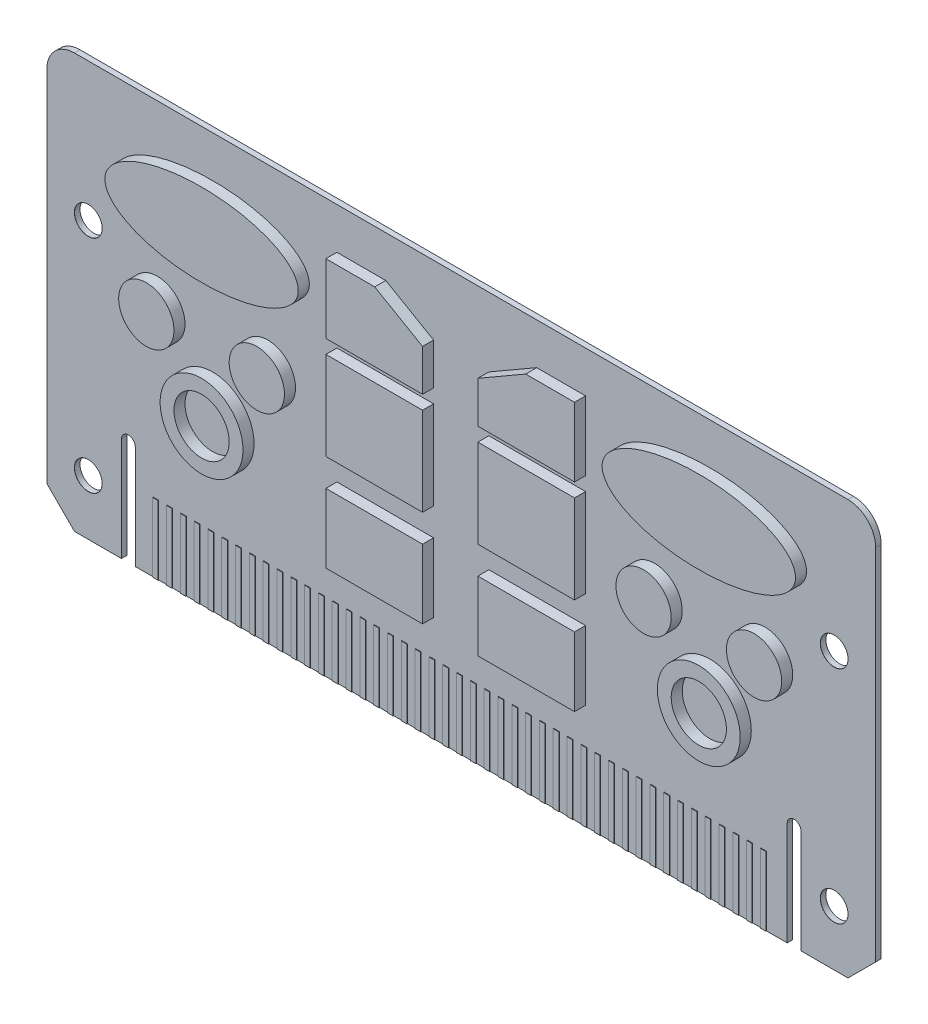
SolidWorks part; units mm, degrees
ref_plane "Front Plane" through (0, 0, 0) normal (0, 0, 1) x (1, 0, 0)
ref_plane "Top Plane" through (0, 0, 0) normal (0, 1, 0) x (1, 0, 0)
ref_plane "Right Plane" through (0, 0, 0) normal (1, 0, 0) x (0, 0, -1)
sketch "Sketch1" plane through (0, 0, 0) normal (0, 0, 1) x (1, 0, 0)
  line L0 (-300, 150) -> (-300, 0)
  line L1 (-300, 0) -> (0, 0)
  line L2 (0, 0) -> (0, 150)
  line L3 (0, 150) -> (-300, 150)
  dimension "D1" = 300
  dimension "D2" = 150
extrude "PCB Base" add sketch "Sketch1" along normal mid plane 2 contours L3 L0 L1 L2
sketch "Sketch3" plane through (0, 0, -1) normal (0, 0, -1) x (-1, 0, 0)
  line L0 (300, 0) -> (0, 0) construction
  line L1 (0, 0) -> (0, 150) construction
  line L2 (300, 150) -> (300, 0) construction
  line L3 (300, 0) -> (0, 0) construction
  line L4 (105, 38) -> (140, 38)
  line L5 (105, 38) -> (105, 63)
  line L6 (105, 63) -> (140, 63)
  line L7 (140, 38) -> (140, 63)
  line L8 (105, 73) -> (140, 73)
  line L9 (105, 73) -> (105, 105)
  line L10 (105, 105) -> (140, 105)
  line L11 (140, 73) -> (140, 105)
  line L12 (105, 110) -> (140, 110)
  line L13 (105, 110) -> (105, 135)
  line L14 (105, 135) -> (122.6795, 135)
  line L15 (140, 110) -> (140, 125)
  line L16 (140, 125) -> (122.6795, 135)
  line L17 (150, 150) -> (150, 0) construction
  line L18 (0, 150) -> (300, 150) construction
  line L19 (160, 125) -> (177.3205, 135)
  line L20 (160, 110) -> (160, 125)
  line L21 (195, 135) -> (177.3205, 135)
  line L22 (195, 110) -> (195, 135)
  line L23 (195, 110) -> (160, 110)
  line L24 (160, 73) -> (160, 105)
  line L25 (195, 105) -> (160, 105)
  line L26 (195, 73) -> (195, 105)
  line L27 (195, 73) -> (160, 73)
  line L28 (160, 38) -> (160, 63)
  line L29 (195, 63) -> (160, 63)
  line L30 (195, 38) -> (195, 63)
  line L31 (195, 38) -> (160, 38)
  circle A0 centre (40, 85) radius 10
  circle A1 centre (80, 85) radius 10
  circle A2 centre (60, 60) radius 15
  circle A3 centre (60, 60) radius 10
  circle A4 centre (240, 60) radius 10
  circle A5 centre (240, 60) radius 15
  circle A6 centre (220, 85) radius 10
  circle A7 centre (260, 85) radius 10
  ellipse E0 centre (60, 120) end of major axis (95, 120) minor radius 15
  ellipse E1 centre (240, 120) end of major axis (205, 120) minor radius 15
  dimension "D1" = 40
  dimension "D2" = 20
  dimension "D3" = 40
  dimension "D5" = 30
  dimension "D8" = 5
  dimension "D4" = 85
  dimension "D6" = 60
  dimension "D7" = 60
  dimension "D9" = 60
  dimension "D10" = 120
  dimension "D11" = 70
  dimension "D12" = 30
  dimension "D13" = 25
  dimension "D14" = 38
  dimension "D15" = 110
  dimension "32mm" = 32
  dimension "D16" = 73
  dimension "D17" = 135
  dimension "D18" = 160
  dimension "D19" = 195
  dimension "D20" = 125
  dimension "D21" = 120
extrude "PCB chips" add sketch "Sketch3" along normal blind 4
mirror "mirror chips" about plane through (0, 0, 0) normal (0, 0, 1) of "PCB chips"
sketch "Sketch4" plane through (0, 0, 1) normal (0, 0, 1) x (1, 0, 0)
  line L0 (-273, 37.5) -> (-273, 0)
  line L1 (-300, 0) -> (0, 0) construction
  line L2 (-268, 37.5) -> (-268, 0)
  line L3 (-300, 150) -> (-300, 0) construction
  line L4 (-273, 0) -> (-268, 0)
  line L5 (-29.5, -3.3575) -> (-29.5, 37.5) construction
  line L6 (-32, -3.3575) -> (-32, 37.5)
  line L7 (-27, -3.3575) -> (-27, 37.5)
  line L8 (-150, 150) -> (-150, 0) construction
  line L9 (0, 150) -> (-300, 150) construction
  arc A0 (-273, 37.5) -> (-268, 37.5) centre (-270.5, 37.5) cw
  arc A1 (-32, -3.3575) -> (-27, -3.3575) centre (-29.5, -3.3575) ccw
  arc A2 (-27, 37.5) -> (-32, 37.5) centre (-29.5, 37.5) ccw
  point P11 (-29.5, 17.0713)
  dimension "D4" = 2.5
  dimension "D1" = 5
  dimension "D2" = 27
  dimension "D3" = 40
extrude "slot cut" cut sketch "Sketch4" against normal blind 10
hole_wizard "Ø10.0mm Dowel Hole1" positions "Sketch6" profile "Sketch7" hole size "Ø10.0" standard "ANSI Metric"
sketch "Sketch6" plane through (0, 0, 1) normal (0, 0, 1) x (1, 0, 0)
  line L0 (-300, 0) -> (-273, 0) construction
  line L1 (-300, 150) -> (-300, 0) construction
  line L2 (-150, 150) -> (-150, 0) construction
  line L3 (0, 150) -> (-300, 150) construction
  line L4 (-268, 0) -> (-32, 0) construction
  point P0 (-285, 100)
  point P2 (-285, 20)
  point P4 (-15, 20)
  point P6 (-15, 100)
  dimension "D1" = 20
  dimension "D2" = 100
  dimension "D3" = 15
sketch "Sketch7" plane through (-285, 100, 1) normal (1, 0, 0) x (0, -1, 0)
  line L0 (0, 0) -> (0, 13.0043)
  line L1 (0, 13.0043) -> (5, 10)
  line L2 (5, 10) -> (5, 0.025)
  line L3 (5, 0.025) -> (5.025, 0)
  line L5 (5.025, 0) -> (0, 0)
  line L6 (-5, 0.025) -> (-5.025, 0) construction
  line L10 (0, 13.0043) -> (-5, 10) construction
  line L11 (0, -6.35) -> (0, 107.95) construction
  dimension "Hole Dia." = 10
  dimension "Hole Depth" = 10
  dimension "Near C'Sink Dia." = 10.05
  dimension "Near C'Sink Angle" = 90
  dimension "Drill Angle" = 118
sketch "Sketch8" plane through (0, 0, 1) normal (0, 0, 1) x (1, 0, 0)
  line L0 (-268, 0) -> (-32, 0) construction
  line L1 (-261.5, 25) -> (-259.5, 25)
  line L2 (-261.5, 25) -> (-261.5, 0)
  line L3 (-261.5, 0) -> (-259.5, 0)
  line L4 (-259.5, 25) -> (-259.5, 0)
  line L5 (-256.5, 25) -> (-256.5, 0)
  line L6 (-256.5, 25) -> (-254.5, 25)
  line L7 (-254.5, 25) -> (-254.5, 0)
  line L8 (-256.5, 0) -> (-254.5, 0)
  line L9 (-251.5, 25) -> (-251.5, 0)
  line L10 (-251.5, 25) -> (-249.5, 25)
  line L11 (-249.5, 25) -> (-249.5, 0)
  line L12 (-251.5, 0) -> (-249.5, 0)
  line L13 (-246.5, 25) -> (-246.5, 0)
  line L14 (-246.5, 25) -> (-244.5, 25)
  line L15 (-244.5, 25) -> (-244.5, 0)
  line L16 (-246.5, 0) -> (-244.5, 0)
  line L17 (-241.5, 25) -> (-241.5, 0)
  line L18 (-241.5, 25) -> (-239.5, 25)
  line L19 (-239.5, 25) -> (-239.5, 0)
  line L20 (-241.5, 0) -> (-239.5, 0)
  line L21 (-236.5, 25) -> (-236.5, 0)
  line L22 (-236.5, 25) -> (-234.5, 25)
  line L23 (-234.5, 25) -> (-234.5, 0)
  line L24 (-236.5, 0) -> (-234.5, 0)
  line L25 (-231.5, 25) -> (-231.5, 0)
  line L26 (-231.5, 25) -> (-229.5, 25)
  line L27 (-229.5, 25) -> (-229.5, 0)
  line L28 (-231.5, 0) -> (-229.5, 0)
  line L29 (-226.5, 25) -> (-226.5, 0)
  line L30 (-226.5, 25) -> (-224.5, 25)
  line L31 (-224.5, 25) -> (-224.5, 0)
  line L32 (-226.5, 0) -> (-224.5, 0)
  line L33 (-221.5, 25) -> (-221.5, 0)
  line L34 (-221.5, 25) -> (-219.5, 25)
  line L35 (-219.5, 25) -> (-219.5, 0)
  line L36 (-221.5, 0) -> (-219.5, 0)
  line L37 (-216.5, 25) -> (-216.5, 0)
  line L38 (-216.5, 25) -> (-214.5, 25)
  line L39 (-214.5, 25) -> (-214.5, 0)
  line L40 (-216.5, 0) -> (-214.5, 0)
  line L41 (-211.5, 25) -> (-211.5, 0)
  line L42 (-211.5, 25) -> (-209.5, 25)
  line L43 (-209.5, 25) -> (-209.5, 0)
  line L44 (-211.5, 0) -> (-209.5, 0)
  line L45 (-206.5, 25) -> (-206.5, 0)
  line L46 (-206.5, 25) -> (-204.5, 25)
  line L47 (-204.5, 25) -> (-204.5, 0)
  line L48 (-206.5, 0) -> (-204.5, 0)
  line L49 (-201.5, 25) -> (-201.5, 0)
  line L50 (-201.5, 25) -> (-199.5, 25)
  line L51 (-199.5, 25) -> (-199.5, 0)
  line L52 (-201.5, 0) -> (-199.5, 0)
  line L53 (-196.5, 25) -> (-196.5, 0)
  line L54 (-196.5, 25) -> (-194.5, 25)
  line L55 (-194.5, 25) -> (-194.5, 0)
  line L56 (-196.5, 0) -> (-194.5, 0)
  line L57 (-191.5, 25) -> (-191.5, 0)
  line L58 (-191.5, 25) -> (-189.5, 25)
  line L59 (-189.5, 25) -> (-189.5, 0)
  line L60 (-191.5, 0) -> (-189.5, 0)
  line L61 (-186.5, 25) -> (-186.5, 0)
  line L62 (-186.5, 25) -> (-184.5, 25)
  line L63 (-184.5, 25) -> (-184.5, 0)
  line L64 (-186.5, 0) -> (-184.5, 0)
  line L65 (-181.5, 25) -> (-181.5, 0)
  line L66 (-181.5, 25) -> (-179.5, 25)
  line L67 (-179.5, 25) -> (-179.5, 0)
  line L68 (-181.5, 0) -> (-179.5, 0)
  line L69 (-176.5, 25) -> (-176.5, 0)
  line L70 (-176.5, 25) -> (-174.5, 25)
  line L71 (-174.5, 25) -> (-174.5, 0)
  line L72 (-176.5, 0) -> (-174.5, 0)
  line L73 (-171.5, 25) -> (-171.5, 0)
  line L74 (-171.5, 25) -> (-169.5, 25)
  line L75 (-169.5, 25) -> (-169.5, 0)
  line L76 (-171.5, 0) -> (-169.5, 0)
  line L77 (-166.5, 25) -> (-166.5, 0)
  line L78 (-166.5, 25) -> (-164.5, 25)
  line L79 (-164.5, 25) -> (-164.5, 0)
  line L80 (-166.5, 0) -> (-164.5, 0)
  line L81 (-161.5, 25) -> (-161.5, 0)
  line L82 (-161.5, 25) -> (-159.5, 25)
  line L83 (-159.5, 25) -> (-159.5, 0)
  line L84 (-161.5, 0) -> (-159.5, 0)
  line L85 (-156.5, 25) -> (-156.5, 0)
  line L86 (-156.5, 25) -> (-154.5, 25)
  line L87 (-154.5, 25) -> (-154.5, 0)
  line L88 (-156.5, 0) -> (-154.5, 0)
  line L89 (-151.5, 25) -> (-151.5, 0)
  line L90 (-151.5, 25) -> (-149.5, 25)
  line L91 (-149.5, 25) -> (-149.5, 0)
  line L92 (-151.5, 0) -> (-149.5, 0)
  line L93 (-146.5, 25) -> (-146.5, 0)
  line L94 (-146.5, 25) -> (-144.5, 25)
  line L95 (-144.5, 25) -> (-144.5, 0)
  line L96 (-146.5, 0) -> (-144.5, 0)
  line L97 (-141.5, 25) -> (-141.5, 0)
  line L98 (-141.5, 25) -> (-139.5, 25)
  line L99 (-139.5, 25) -> (-139.5, 0)
  line L100 (-141.5, 0) -> (-139.5, 0)
  line L101 (-136.5, 25) -> (-136.5, 0)
  line L102 (-136.5, 25) -> (-134.5, 25)
  line L103 (-134.5, 25) -> (-134.5, 0)
  line L104 (-136.5, 0) -> (-134.5, 0)
  line L105 (-131.5, 25) -> (-131.5, 0)
  line L106 (-131.5, 25) -> (-129.5, 25)
  line L107 (-129.5, 25) -> (-129.5, 0)
  line L108 (-131.5, 0) -> (-129.5, 0)
  line L109 (-126.5, 25) -> (-126.5, 0)
  line L110 (-126.5, 25) -> (-124.5, 25)
  line L111 (-124.5, 25) -> (-124.5, 0)
  line L112 (-126.5, 0) -> (-124.5, 0)
  line L113 (-121.5, 25) -> (-121.5, 0)
  line L114 (-121.5, 25) -> (-119.5, 25)
  line L115 (-119.5, 25) -> (-119.5, 0)
  line L116 (-121.5, 0) -> (-119.5, 0)
  line L117 (-116.5, 25) -> (-116.5, 0)
  line L118 (-116.5, 25) -> (-114.5, 25)
  line L119 (-114.5, 25) -> (-114.5, 0)
  line L120 (-116.5, 0) -> (-114.5, 0)
  line L121 (-111.5, 25) -> (-111.5, 0)
  line L122 (-111.5, 25) -> (-109.5, 25)
  line L123 (-109.5, 25) -> (-109.5, 0)
  line L124 (-111.5, 0) -> (-109.5, 0)
  line L125 (-106.5, 25) -> (-106.5, 0)
  line L126 (-106.5, 25) -> (-104.5, 25)
  line L127 (-104.5, 25) -> (-104.5, 0)
  line L128 (-106.5, 0) -> (-104.5, 0)
  line L129 (-101.5, 25) -> (-101.5, 0)
  line L130 (-101.5, 25) -> (-99.5, 25)
  line L131 (-99.5, 25) -> (-99.5, 0)
  line L132 (-101.5, 0) -> (-99.5, 0)
  line L133 (-96.5, 25) -> (-96.5, 0)
  line L134 (-96.5, 25) -> (-94.5, 25)
  line L135 (-94.5, 25) -> (-94.5, 0)
  line L136 (-96.5, 0) -> (-94.5, 0)
  line L137 (-91.5, 25) -> (-91.5, 0)
  line L138 (-91.5, 25) -> (-89.5, 25)
  line L139 (-89.5, 25) -> (-89.5, 0)
  line L140 (-91.5, 0) -> (-89.5, 0)
  line L141 (-86.5, 25) -> (-86.5, 0)
  line L142 (-86.5, 25) -> (-84.5, 25)
  line L143 (-84.5, 25) -> (-84.5, 0)
  line L144 (-86.5, 0) -> (-84.5, 0)
  line L145 (-81.5, 25) -> (-81.5, 0)
  line L146 (-81.5, 25) -> (-79.5, 25)
  line L147 (-79.5, 25) -> (-79.5, 0)
  line L148 (-81.5, 0) -> (-79.5, 0)
  line L149 (-76.5, 25) -> (-76.5, 0)
  line L150 (-76.5, 25) -> (-74.5, 25)
  line L151 (-74.5, 25) -> (-74.5, 0)
  line L152 (-76.5, 0) -> (-74.5, 0)
  line L153 (-71.5, 25) -> (-71.5, 0)
  line L154 (-71.5, 25) -> (-69.5, 25)
  line L155 (-69.5, 25) -> (-69.5, 0)
  line L156 (-71.5, 0) -> (-69.5, 0)
  line L157 (-66.5, 25) -> (-66.5, 0)
  line L158 (-66.5, 25) -> (-64.5, 25)
  line L159 (-64.5, 25) -> (-64.5, 0)
  line L160 (-66.5, 0) -> (-64.5, 0)
  line L161 (-61.5, 25) -> (-61.5, 0)
  line L162 (-61.5, 25) -> (-59.5, 25)
  line L163 (-59.5, 25) -> (-59.5, 0)
  line L164 (-61.5, 0) -> (-59.5, 0)
  line L165 (-56.5, 25) -> (-56.5, 0)
  line L166 (-56.5, 25) -> (-54.5, 25)
  line L167 (-54.5, 25) -> (-54.5, 0)
  line L168 (-56.5, 0) -> (-54.5, 0)
  line L169 (-51.5, 25) -> (-51.5, 0)
  line L170 (-51.5, 25) -> (-49.5, 25)
  line L171 (-49.5, 25) -> (-49.5, 0)
  line L172 (-51.5, 0) -> (-49.5, 0)
  line L173 (-46.5, 25) -> (-46.5, 0)
  line L174 (-46.5, 25) -> (-44.5, 25)
  line L175 (-44.5, 25) -> (-44.5, 0)
  line L176 (-46.5, 0) -> (-44.5, 0)
  line L177 (-41.5, 25) -> (-41.5, 0)
  line L178 (-41.5, 25) -> (-39.5, 25)
  line L179 (-39.5, 25) -> (-39.5, 0)
  line L180 (-41.5, 0) -> (-39.5, 0)
  point P6 (-260.5, 25)
  dimension "D1" = 25
  dimension "D2" = 2
  dimension "D3" = 6.5
  dimension "D5" = 3
  dimension "D4" = 45
extrude "down contact" add sketch "Sketch8" along normal blind 0.2
chamfer "Chamfer1" distance 10 angle 45 2 edges at (-300, 0, 0) (0, 0, 0)
fillet "fillet" radius 10 2 edges at (0, 150, 0) (-300, 150, 0)
